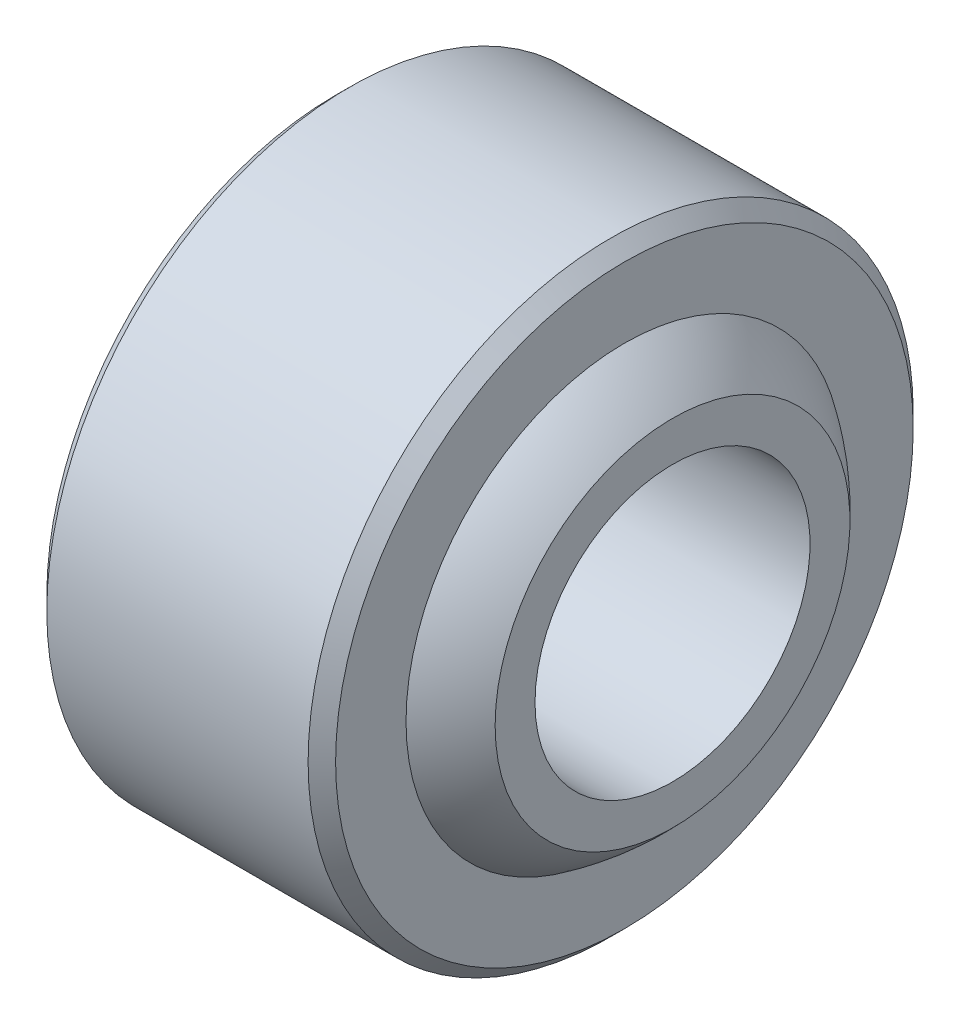
SolidWorks part; units mm, degrees
ref_plane "Płaszczyzna przednia" through (0, 0, 0) normal (0, 0, 1) x (1, 0, 0)
ref_plane "Płaszczyzna górna" through (0, 0, 0) normal (0, 1, 0) x (1, 0, 0)
ref_plane "Płaszczyzna prawa" through (0, 0, 0) normal (1, 0, 0) x (0, 0, -1)
sketch "Szkic1" plane through (0, 0, 0) normal (0, 0, 1) x (1, 0, 0)
  line L0 (-7, 0) -> (7, 0)
  line L1 (-7, 0) -> (-7, 1.45)
  line L2 (0, 0) -> (0, 6) construction
  line L3 (7, 0) -> (7, 1.45)
  line L4 (-7.6504, -5) -> (7, -5) construction
  line L5 (-5.25, 6) -> (5.25, 6)
  line L6 (-5.25, 6) -> (-5.25, 2.9398)
  line L7 (5.25, 6) -> (5.25, 2.9398)
  arc A0 (7, 1.45) -> (5.25, 2.9398) centre (0, -5) ccw
  arc A2 (-5.25, 2.9398) -> (-7, 1.45) centre (0, -5) ccw
  dimension "D4" = 6
  dimension "D1" = 5
  dimension "D2" = 7
  dimension "D3" = 1.45
  dimension "D5" = 5.25
  dimension "D6" = 3.0602
revolve "Obrót1" add sketch "Szkic1" angle 360 about L4
chamfer "Sfazowanie1" distance 0.5 angle 45 2 edges at (-5.25, -5, 11) (5.25, -5, 11)
